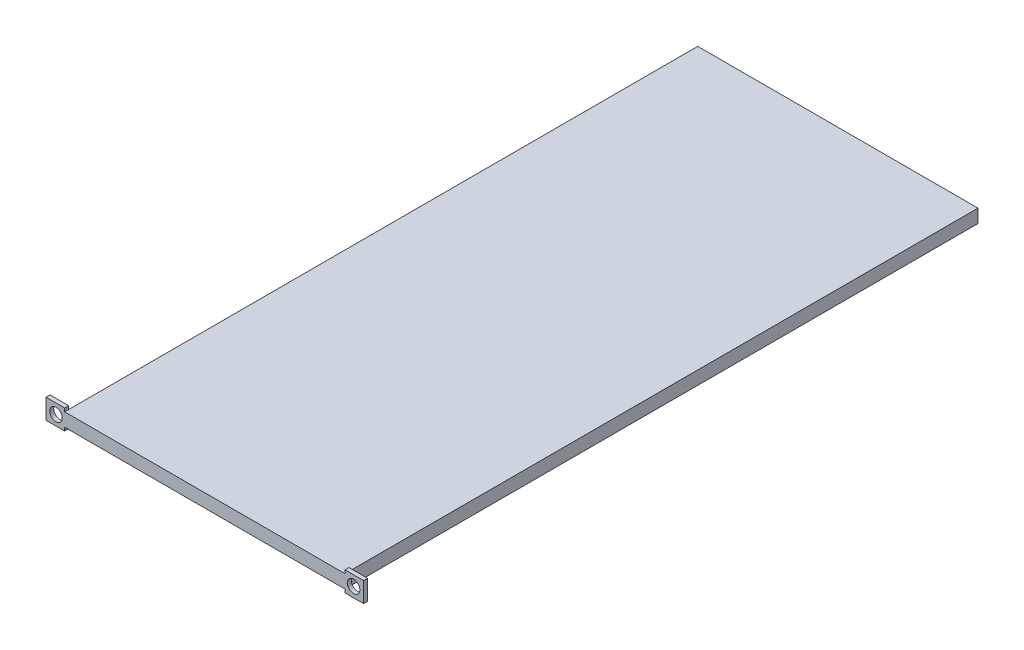
SolidWorks part; units mm, degrees
ref_plane "Front Plane" through (0, 0, 0) normal (0, 0, 1) x (1, 0, 0)
ref_plane "Top Plane" through (0, 0, 0) normal (0, 1, 0) x (1, 0, 0)
ref_plane "Right Plane" through (0, 0, 0) normal (1, 0, 0) x (0, 0, -1)
sketch "Sketch1" plane through (0, 0, 0) normal (0, 0, 1) x (1, 0, 0)
  line L1 (0, 0) -> (210.29, 0)
  line L2 (0, 0) -> (0, 10)
  line L3 (0, 10) -> (210.29, 10)
  line L4 (210.29, 0) -> (210.29, 10)
  dimension "D1" = 210.29
  dimension "D2" = 10
extrude "Boss-Extrude1" add sketch "Sketch1" along normal blind 475
sketch "Sketch2" plane through (0, 0, 0) normal (-1, 0, 0) x (0, 0, 1)
  line L0 (475, 10) -> (475, 0) construction
  line L1 (475, 12.5) -> (472, 12.5)
  line L2 (475, 12.5) -> (475, -2.5)
  line L3 (475, -2.5) -> (472, -2.5)
  line L4 (472, 12.5) -> (472, -2.5)
  dimension "D1" = 3
  dimension "D2" = 15
  dimension "D3" = 2.5
extrude "Boss-Extrude2" add sketch "Sketch2" along normal blind 14
sketch "Sketch4" plane through (210.29, 0, 0) normal (1, 0, 0) x (0, 0, -1)
  line L1 (-475, 12.5) -> (-472, 12.5)
  line L2 (-475, 12.5) -> (-475, -2.5)
  line L3 (-475, -2.5) -> (-472, -2.5)
  line L4 (-472, 12.5) -> (-472, -2.5)
extrude "Boss-Extrude3" add sketch "Sketch4" along normal blind 14
sketch "Sketch3" plane through (0, 0, 472) normal (0, 0, -1) x (-1, 0, 0)
  line L0 (0, 10) -> (0, 0) construction
  line L1 (-105.145, 44.2026) -> (-105.145, -53.8154) construction
  circle A0 centre (6.5, 5) radius 4.7
  circle A2 centre (-216.79, 5) radius 4.7
  dimension "D1" = 9.4
  dimension "D2" = 6.5
  dimension "D3" = 5
extrude "Cut-Extrude1" cut sketch "Sketch3" against normal blind 13
